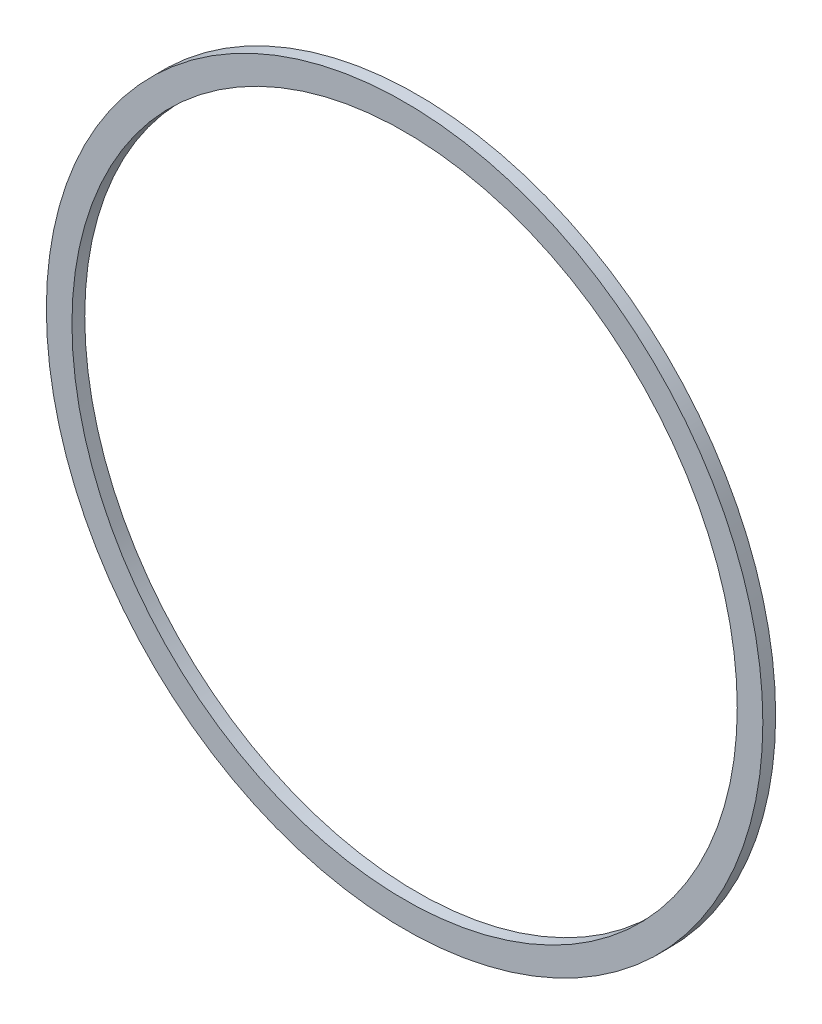
SolidWorks part; units mm, degrees
material "1060-O (SS)"
ref_plane "Ebene vorne" through (0, 0, 0) normal (0, 0, 1) x (1, 0, 0)
ref_plane "Ebene oben" through (0, 0, 0) normal (0, 1, 0) x (1, 0, 0)
ref_plane "Ebene rechts" through (0, 0, 0) normal (1, 0, 0) x (0, 0, -1)
sketch "Sketch1" plane through (0, 0, 0) normal (0, 0, 1) x (1, 0, 0)
  circle A0 centre (0, 0) radius 26
  circle A1 centre (0, 0) radius 28
  dimension "D1" = 2
  dimension "D2" = 52
extrude "Boss-Extrude1" add sketch "Sketch1" along normal blind 1
